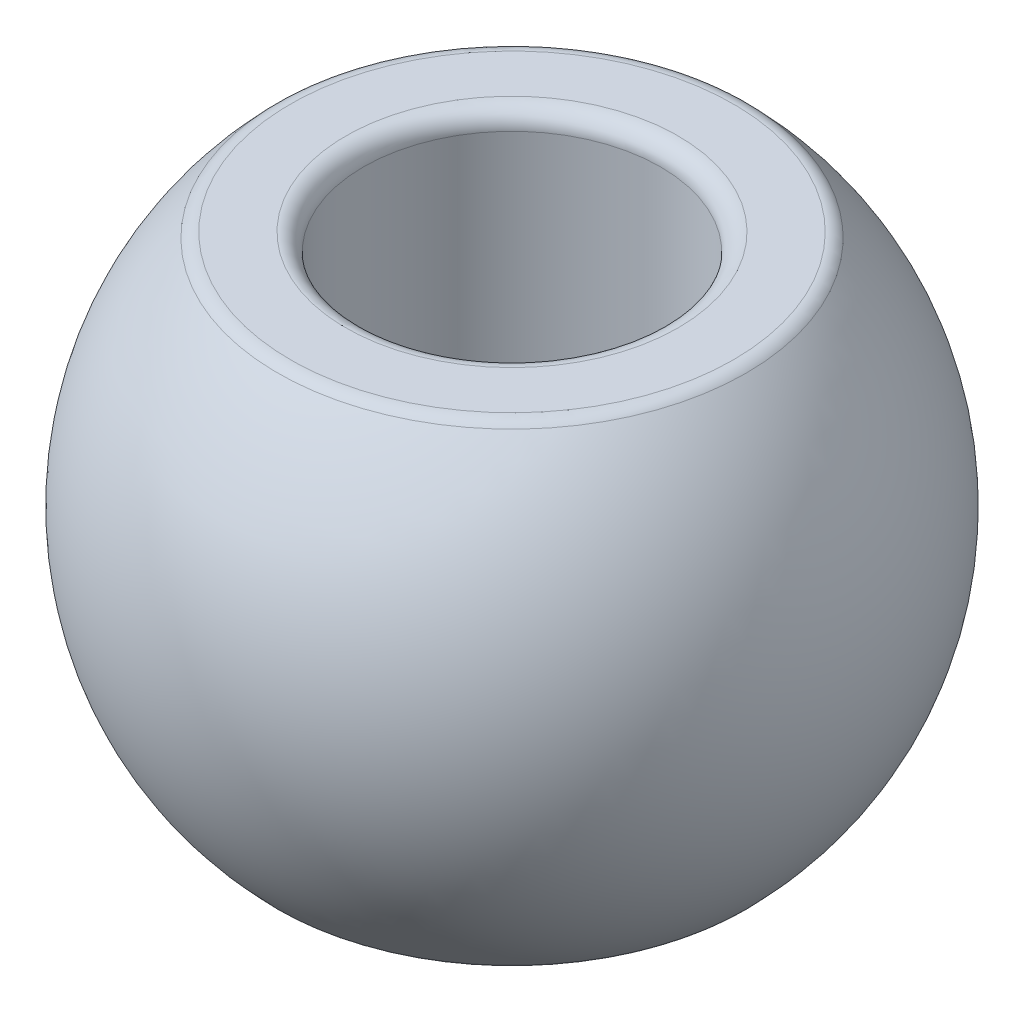
SolidWorks part; units mm, degrees
material "ASTM 52100 Bearing Steel"
ref_plane "Front Plane" through (0, 0, 0) normal (0, 0, 1) x (1, 0, 0)
ref_plane "Top Plane" through (0, 0, 0) normal (0, 1, 0) x (1, 0, 0)
ref_plane "Right Plane" through (0, 0, 0) normal (1, 0, 0) x (0, 0, -1)
sketch "Sketch1" plane through (0, 0, 0) normal (0, 0, 1) x (1, 0, 0)
  line L0 (0, 4) -> (0, -4) construction
  line L1 (0, 4) -> (3.8546, 4) construction
  line L2 (0, -4) -> (3.8546, -4) construction
  line L3 (3.8546, 4) -> (2.5, 4)
  line L4 (2.5, 4) -> (2.5, -4)
  line L5 (2.5, -4) -> (3.8546, -4)
  arc A0 (3.8546, -4) -> (3.8546, 4) centre (0, 0) ccw
  point P3 (0, 0)
  dimension "D1" = 8
  dimension "D2" = 5
  dimension "D3" = 11.11
revolve "Revolve1" add sketch "Sketch1" angle 360 about L0
fillet "Fillet1" radius 0.3 4 edges at (-3.8546, -4, 0) (-3.8546, 4, 0) (-2.5, 4, 0) (-2.5, -4, 0)
equation "\"d\"= \"d3\" + \"Add\""
equation "\"Pitch\"= 1.5"
equation "\"B\" = 8"
equation "\"dk\" = 11.11"
equation "\"Add\"= 0"
equation "\"d3\"= 5"
equation "\"D2@Sketch1\"= \"d\""
equation "\"D3@Sketch1\"=\"dk\""
equation "\"D1@Sketch1\"=\"B\""
